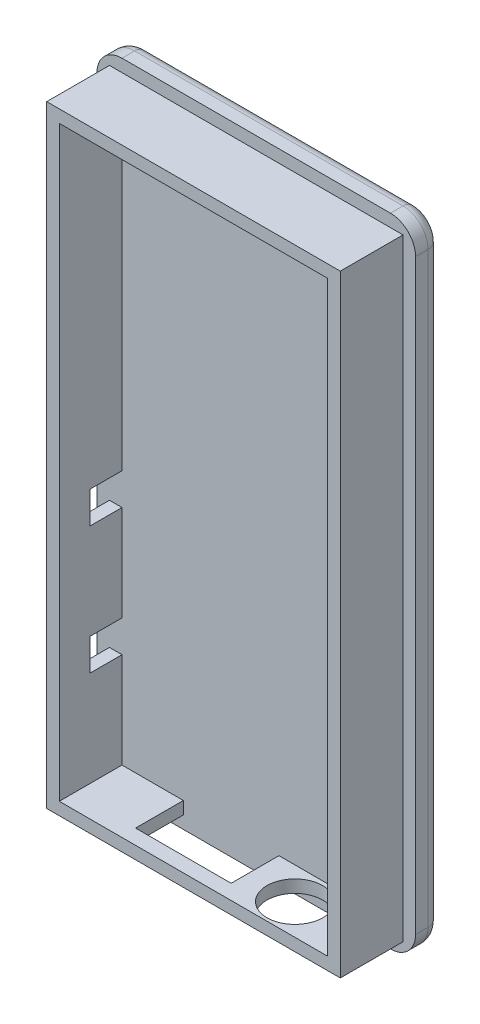
SolidWorks part; units mm, degrees
ref_plane "Front Plane" through (0, 0, 0) normal (0, 0, 1) x (1, 0, 0)
ref_plane "Top Plane" through (0, 0, 0) normal (0, 1, 0) x (1, 0, 0)
ref_plane "Right Plane" through (0, 0, 0) normal (1, 0, 0) x (0, 0, -1)
sketch "Sketch2" plane through (0, 0, 0) normal (0, 0, 1) x (1, 0, 0)
  line L1 (0, 0) -> (25.4, 0)
  line L2 (0, 0) -> (0, 50.8)
  line L3 (0, 50.8) -> (25.4, 50.8)
  line L4 (25.4, 0) -> (25.4, 50.8)
  dimension "D1" = 25.4
  dimension "D2" = 50.8
extrude "Boss-Extrude1" add sketch "Sketch2" along normal blind 2
sketch "Sketch3" plane through (0, 0, 2) normal (0, 0, 1) x (1, 0, 0)
  line L0 (25.4, 50.8) -> (0, 50.8) construction
  line L1 (1, 49.8) -> (24.4, 49.8)
  line L2 (1, 49.8) -> (1, 1)
  line L3 (1, 1) -> (24.4, 1)
  line L4 (24.4, 49.8) -> (24.4, 1)
  line L5 (2, 48.8) -> (23.4, 48.8)
  line L6 (2, 48.8) -> (2, 2)
  line L7 (2, 2) -> (23.4, 2)
  line L8 (23.4, 48.8) -> (23.4, 2)
  line L9 (0, 50.8) -> (0, 0) construction
  line L10 (0, 0) -> (25.4, 0) construction
  line L11 (25.4, 0) -> (25.4, 50.8) construction
  line L12 (25.4, 50.8) -> (0, 50.8)
  line L13 (0, 50.8) -> (0, 0)
  line L14 (0, 0) -> (25.4, 0)
  line L15 (25.4, 0) -> (25.4, 50.8)
  dimension "D1" = 1
  dimension "D2" = 1
  dimension "D3" = 1
  dimension "D4" = 1
  dimension "D5" = 1
  dimension "D6" = 1
  dimension "D7" = 1
  dimension "D8" = 1
extrude "Boss-Extrude2" add sketch "Sketch3" along normal blind 5 contours L4 L1 L2 L3 L5 L8 L7 L6
fillet "Fillet1" radius 2 4 edges at (0, 50.8, 1) (0, 0, 1) (25.4, 0, 1) (25.4, 50.8, 1)
fillet "Fillet2" radius 1 8 edges at (0.5858, 0.5858, 0) (12.7, 0, 0) (24.8142, 0.5858, 0) (25.4, 25.4, 0) (24.8142, 50.2142, 0) (12.7, 50.8, 0) (0.5858, 50.2142, 0) (0, 25.4, 0)
sketch "Sketch5" plane through (0, 1, 0) normal (0, -1, 0) x (1, 0, 0)
  circle A0 centre (18.32, 4.54) radius 2.2225
extrude "Cut-Extrude2" cut sketch "Sketch5" against normal up to next
sketch "Sketch6" plane through (0, 1, 0) normal (0, -1, 0) x (1, 0, 0)
  line L0 (6.89, 5.81) -> (6.89, 2) construction
  line L1 (14.51, 5.81) -> (6.89, 5.81)
  line L2 (14.51, 5.81) -> (14.51, 2)
  line L3 (14.51, 2) -> (6.89, 2)
  line L4 (6.89, 5.81) -> (6.89, 2)
  line L5 (1, 2) -> (24.4, 2) construction
extrude "Cut-Extrude3" cut sketch "Sketch6" against normal up to next
sketch "Sketch7" plane through (1, 0, 0) normal (-1, 0, 0) x (0, 0, 1)
  line L0 (2, 49.8) -> (2, 1) construction
  line L1 (2, 12.16) -> (4.54, 12.16)
  line L2 (2, 12.16) -> (2, 9.62)
  line L3 (2, 9.62) -> (4.54, 9.62)
  line L4 (4.54, 12.16) -> (4.54, 9.62)
  line L5 (4.54, 12.16) -> (2, 12.16) construction
  line L6 (2, 9.62) -> (4.54, 9.62) construction
  line L7 (4.54, 9.62) -> (4.54, 12.16) construction
  line L9 (2, 22.32) -> (4.54, 22.32)
  line L10 (2, 22.32) -> (2, 19.78)
  line L11 (2, 19.78) -> (4.54, 19.78)
  line L12 (4.54, 22.32) -> (4.54, 19.78)
extrude "Cut-Extrude4" cut sketch "Sketch7" against normal up to next
equation "\"width\"=1"
equation "\"D1@Sketch2\"=\"width\""
equation "\"length\"=2"
equation "\"D2@Sketch2\"=\"length\""
equation "\"container_thickness\"=0.0787402"
equation "\"D1@Boss-Extrude1\"=\"container_thickness\""
equation "\"lip_thickness\"=0.0393701"
equation "\"D1@Sketch3\"=\"lip_thickness\""
equation "\"D2@Sketch3\"=\"lip_thickness\""
equation "\"D3@Sketch3\"=\"lip_thickness\""
equation "\"D4@Sketch3\"=\"lip_thickness\""
equation "\"D5@Sketch3\"=\"lip_thickness\""
equation "\"D6@Sketch3\"=\"lip_thickness\""
equation "\"D7@Sketch3\"=\"lip_thickness\""
equation "\"D8@Sketch3\"=\"lip_thickness\""
equation "\"lip_height\"= 5mm"
equation "\"D1@Boss-Extrude2\"=\"lip_height\""
equation "\"side_fillet\"= 2mm"
equation "\"D1@Fillet1\"=\"side_fillet\""
equation "\"face_fillet\"= 1mm"
equation "\"D1@Fillet2\"=\"face_fillet\""
